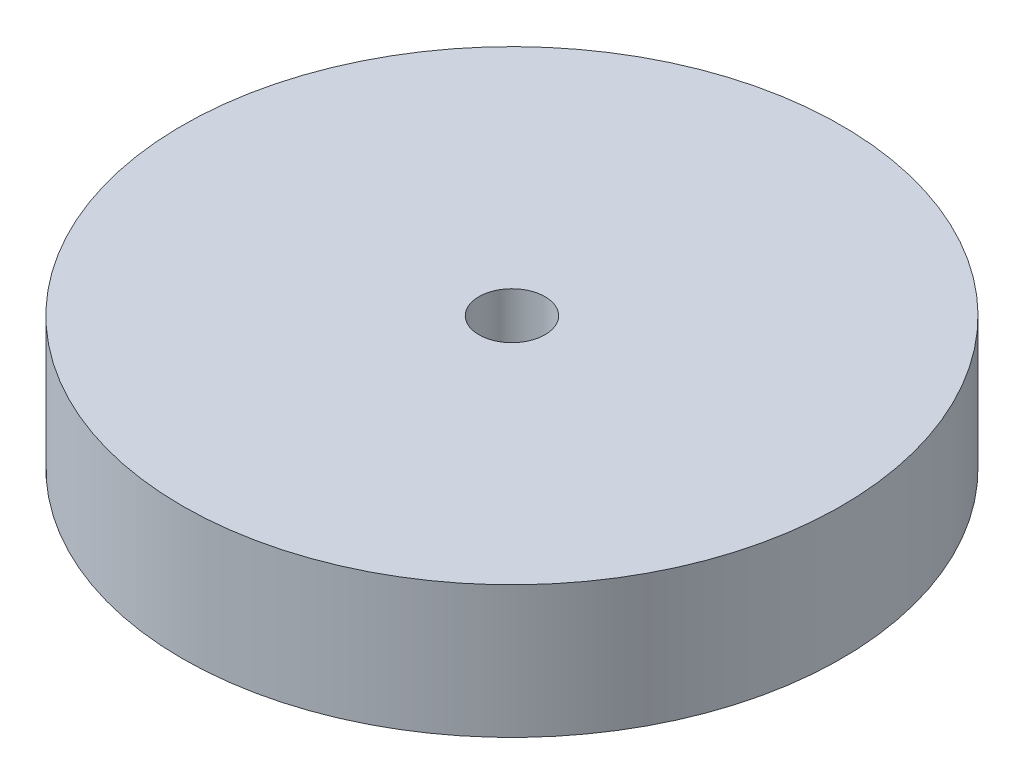
SolidWorks part; units mm, degrees
ref_plane "Front Plane" through (0, 0, 0) normal (0, 0, 1) x (1, 0, 0)
ref_plane "Top Plane" through (0, 0, 0) normal (0, 1, 0) x (1, 0, 0)
ref_plane "Right Plane" through (0, 0, 0) normal (1, 0, 0) x (0, 0, -1)
sketch "Sketch1" plane through (0, 0, 0) normal (0, 1, 0) x (1, 0, 0)
  circle A1 centre (0, 0) radius 1.27
  circle A2 centre (0, 0) radius 12.6629
extrude "Boss-Extrude2" add sketch "Sketch1" along normal blind 5.08
